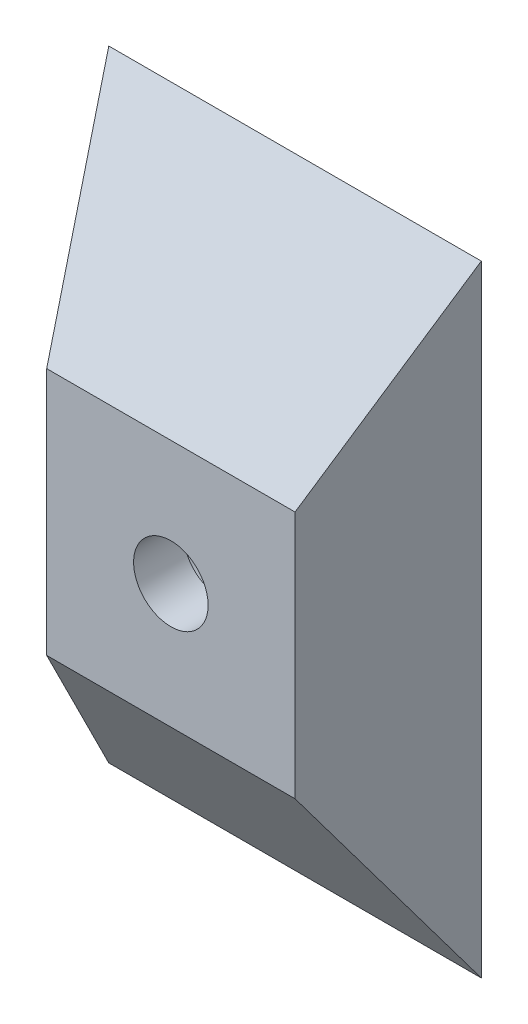
SolidWorks part; units mm, degrees
ref_plane "Alzado" through (0, 0, 0) normal (0, 0, 1) x (1, 0, 0)
ref_plane "Planta" through (0, 0, 0) normal (0, 1, 0) x (1, 0, 0)
ref_plane "Vista lateral" through (0, 0, 0) normal (1, 0, 0) x (0, 0, -1)
sketch "Croquis1" plane through (0, 0, 0) normal (0, 0, 1) x (1, 0, 0)
  line L1 (-7.5, -12.5) -> (7.5, -12.5)
  line L2 (-7.5, -12.5) -> (-7.5, 12.5)
  line L3 (-7.5, 12.5) -> (7.5, 12.5)
  line L4 (7.5, -12.5) -> (7.5, 12.5)
  line L5 (-7.5, -12.5) -> (7.5, 12.5) construction
  line L6 (-7.5, 12.5) -> (7.5, -12.5) construction
  point P0 (0, 0)
  dimension "D1" = 15
  dimension "D2" = 25
ref_plane "Plano1" through (0, 0, 5) normal (0, 0, 1) x (1, 0, 0)
sketch "Croquis9" plane through (0, 0, 5) normal (0, 0, 1) x (1, 0, 0)
  line L1 (-5, 5) -> (5, 5)
  line L2 (-5, 5) -> (-5, -5)
  line L3 (-5, -5) -> (5, -5)
  line L4 (5, 5) -> (5, -5)
  line L5 (-5, 5) -> (5, -5) construction
  line L6 (-5, -5) -> (5, 5) construction
  point P0 (0, 0)
  dimension "D1" = 10
loft "Recubrir1" add profiles "Croquis1", "Croquis9"
sketch "Croquis10" plane through (0, 0, 5) normal (0, 0, 1) x (1, 0, 0)
  circle A0 centre (0, 0) radius 1.5
  dimension "D1" = 3
extrude "Cortar-Extruir1" cut sketch "Croquis10" against normal blind 5
sketch "Croquis11" plane through (0, 0, 0) normal (0, 0, -1) x (-1, 0, 0)
  circle A0 centre (0, 0) radius 2.5
  dimension "D1" = 5
extrude "Cortar-Extruir2" cut sketch "Croquis11" against normal blind 3
